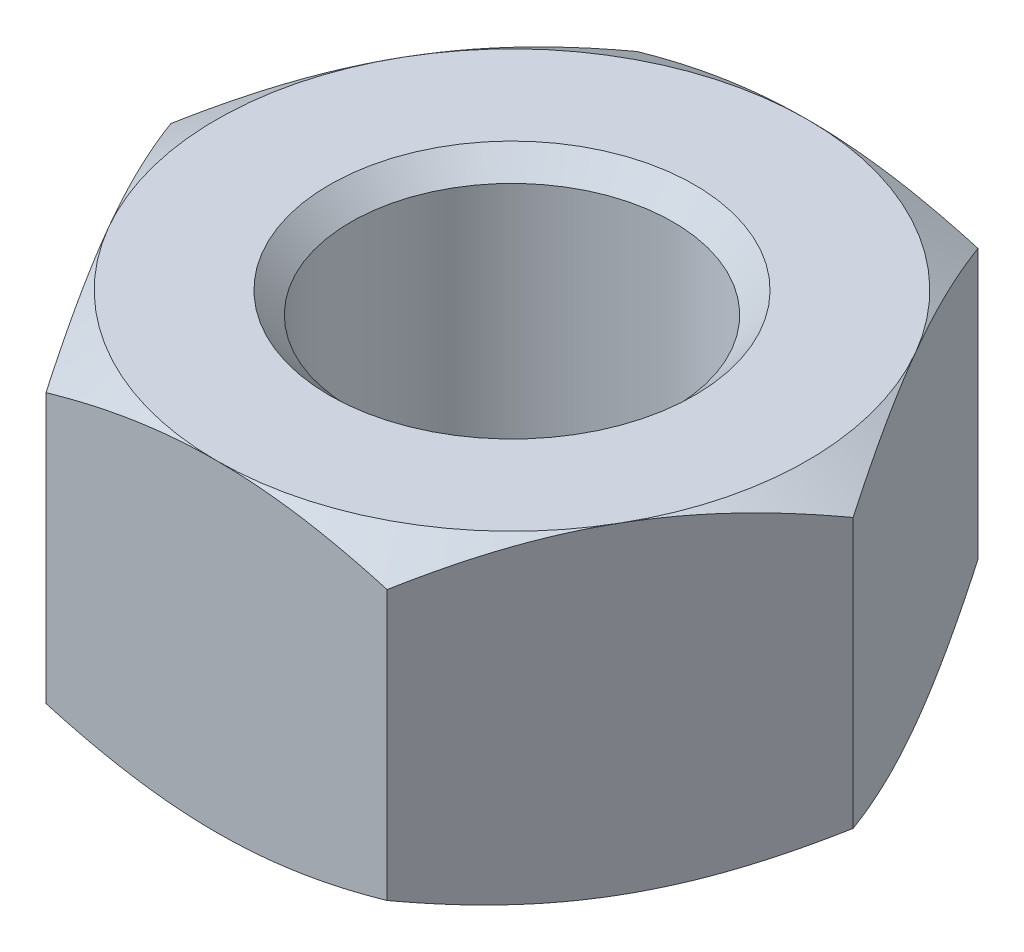
SolidWorks part; units mm, degrees
ref_plane "Front Plane" through (0, 0, 0) normal (0, 0, 1) x (1, 0, 0)
ref_plane "Top Plane" through (0, 0, 0) normal (0, 1, 0) x (1, 0, 0)
ref_plane "Right Plane" through (0, 0, 0) normal (1, 0, 0) x (0, 0, -1)
sketch "Sketch1" plane through (0, 0, 0) normal (0, 1, 0) x (1, 0, 0)
  line L1 (10.0893, 0) -> (5.0447, 8.7376)
  line L2 (5.0447, 8.7376) -> (-5.0447, 8.7376)
  line L3 (-5.0447, 8.7376) -> (-10.0893, 0)
  line L4 (-10.0893, 0) -> (-5.0447, -8.7376)
  line L5 (-5.0447, -8.7376) -> (5.0447, -8.7376)
  line L6 (5.0447, -8.7376) -> (10.0893, 0)
  circle A0 centre (0, 0) radius 8.7376 construction
  circle A1 centre (0, 0) radius 4.7625
  dimension "D1" = 17.4752
  dimension "D3" = 9.525
  dimension "D2" = 8.7376
extrude "Boss-Extrude1" add sketch "Sketch1" along normal blind 9.525
sketch "Sketch2" plane through (0, 9.525, 0) normal (0, 1, 0) x (1, 0, 0)
  circle A0 centre (0, 0) radius 8.7376
  dimension "D1" = 17.4752
extrude "Cut-Extrude1" cut sketch "Sketch2" against normal blind 9.525 draft 60 flip side to cut contours A0
sketch "Sketch3" plane through (0, 0, 0) normal (0, -1, 0) x (1, 0, 0)
  circle A0 centre (0, 0) radius 8.7376
  dimension "D1" = 17.4752
extrude "Cut-Extrude2" cut sketch "Sketch3" against normal blind 9.525 draft 60 flip side to cut
chamfer "Chamfer1" distance 0.635 angle 45 2 edges at (0, 9.525, 4.7625) (0, 0, 4.7625)
